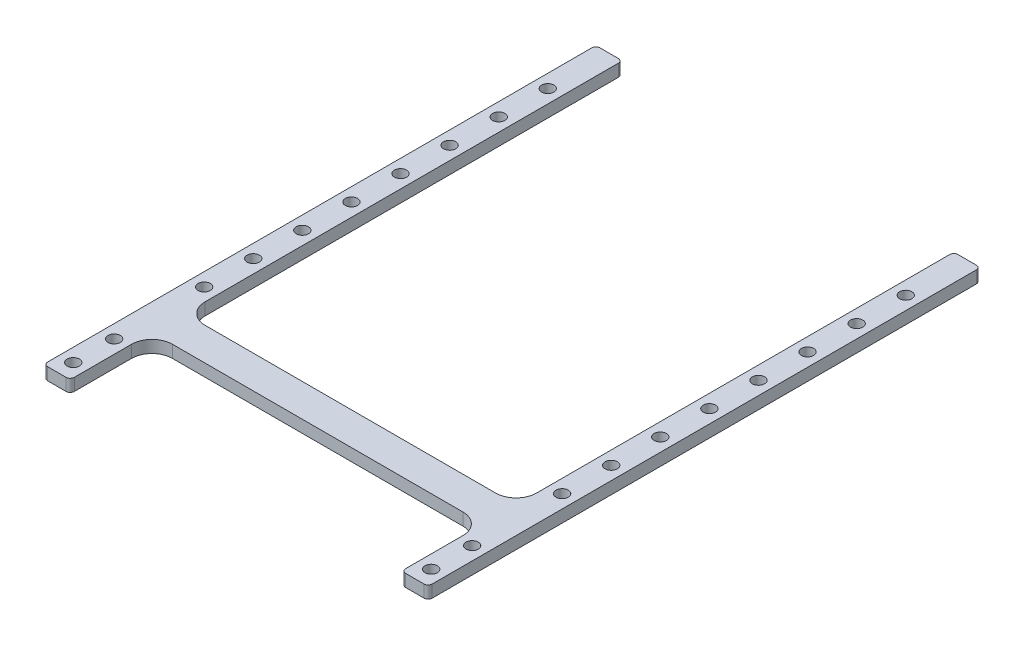
SolidWorks part; units mm, degrees
ref_plane "Front Plane" through (0, 0, 0) normal (0, 0, 1) x (1, 0, 0)
ref_plane "Top Plane" through (0, 0, 0) normal (0, 1, 0) x (1, 0, 0)
ref_plane "Right Plane" through (0, 0, 0) normal (1, 0, 0) x (0, 0, -1)
sketch "Sketch1" plane through (0, 0, 0) normal (0, 1, 0) x (1, 0, 0)
  line L6 (-221.7997, -37.6745) -> (-221.7997, -32.6745) construction
  line L9 (-226.7997, -52.6745) -> (-233.2997, -52.6745)
  line L10 (-233.2997, 67.3255) -> (-233.2997, -52.6745)
  line L13 (-145.7997, -52.6745) -> (-139.2997, -52.6745)
  line L14 (-139.2997, 67.3255) -> (-139.2997, -52.6745)
  line L23 (-150.7997, -37.6745) -> (-150.7997, -32.6745) construction
  line L25 (-226.7997, -37.6745) -> (-221.7997, -37.6745) construction
  line L26 (-186.2997, -37.6745) -> (-186.2997, -32.6745) construction
  line L27 (-221.7997, -24.6745) -> (-221.7997, -19.6745) construction
  line L28 (-221.7997, -19.6745) -> (-150.7997, -19.6745) construction
  line L29 (-150.7997, -19.6745) -> (-150.7997, -24.6745) construction
  line L30 (-145.7997, -52.6745) -> (-145.7997, -37.6745)
  line L31 (-226.7997, -52.6745) -> (-226.7997, -37.6745)
  line L32 (-226.7997, 67.3255) -> (-226.7997, -19.6745)
  line L33 (-145.7997, 67.3255) -> (-145.7997, -19.6745)
  line L34 (-150.7997, -19.6745) -> (-145.7997, -19.6745) construction
  line L35 (-221.7997, -19.6745) -> (-226.7997, -19.6745) construction
  line L36 (-221.7997, -37.6745) -> (-150.7997, -37.6745) construction
  line L37 (-150.7997, -37.6745) -> (-145.7997, -37.6745) construction
  line L38 (-145.7997, 67.3255) -> (-145.7997, 82.3255)
  line L39 (-145.7997, 82.3255) -> (-139.2997, 82.3255)
  line L40 (-139.2997, 67.3255) -> (-139.2997, 82.3255)
  line L41 (-221.7997, -24.6745) -> (-150.7997, -24.6745)
  line L43 (-221.7997, -32.6745) -> (-150.7997, -32.6745)
  line L45 (-233.2997, 67.3255) -> (-233.2997, 82.3255)
  line L46 (-233.2997, 82.3255) -> (-226.7997, 82.3255)
  line L47 (-226.7997, 67.3255) -> (-226.7997, 82.3255)
  arc A4 (-221.7997, -24.6745) -> (-226.7997, -19.6745) centre (-221.7997, -19.6745) cw
  arc A5 (-226.7997, -37.6745) -> (-221.7997, -32.6745) centre (-221.7997, -37.6745) cw
  arc A6 (-150.7997, -32.6745) -> (-145.7997, -37.6745) centre (-150.7997, -37.6745) cw
  arc A7 (-150.7997, -24.6745) -> (-145.7997, -19.6745) centre (-150.7997, -19.6745) ccw
  point P0 (0, 0)
extrude "Boss-Extrude1" add sketch "Sketch1" along normal blind 3
fillet "Fillet1" radius 1 8 edges at (-226.7997, 1.5, 52.6745) (-233.2997, 1.5, 52.6745) (-145.7997, 1.5, 52.6745) (-139.2997, 1.5, 52.6745) (-226.7997, 1.5, -82.3255) (-233.2997, 1.5, -82.3255) (-145.7997, 1.5, -82.3255) (-139.2997, 1.5, -82.3255)
sketch "Sketch2" plane through (0, 3, 0) normal (0, 1, 0) x (1, 0, 0)
  line L0 (-230.0497, 55.3255) -> (-230.0497, 67.3255) construction
  line L2 (-230.0497, -52.6745) -> (-142.5497, -52.6745) construction
  line L3 (-232.2997, -52.6745) -> (-227.7997, -52.6745) construction
  line L4 (-144.7997, -52.6745) -> (-140.2997, -52.6745) construction
  line L5 (-186.2997, -52.6745) -> (-186.2997, 95.8489) construction
  line L6 (-230.0497, 55.3255) -> (-230.0497, 43.3255) construction
  line L7 (-142.5497, 55.3255) -> (-142.5497, 43.3255) construction
  line L8 (-230.0497, 43.3255) -> (-230.0497, 31.3255) construction
  line L9 (-142.5497, 43.3255) -> (-142.5497, 31.3255) construction
  line L10 (-230.0497, 31.3255) -> (-230.0497, 19.3255) construction
  line L11 (-142.5497, 31.3255) -> (-142.5497, 19.3255) construction
  line L12 (-230.0497, 19.3255) -> (-230.0497, 7.3255) construction
  line L13 (-142.5497, 19.3255) -> (-142.5497, 7.3255) construction
  line L14 (-230.0497, 7.3255) -> (-230.0497, -4.6745) construction
  line L15 (-142.5497, 7.3255) -> (-142.5497, -4.6745) construction
  line L16 (-230.0497, -52.6745) -> (-230.0497, -48.6745) construction
  line L17 (-142.5497, -52.6745) -> (-142.5497, -48.6745) construction
  line L18 (-230.0497, -48.6745) -> (-230.0497, -38.6745) construction
  line L19 (-142.5497, -48.6745) -> (-142.5497, -38.6745) construction
  line L20 (-230.0497, -4.6745) -> (-230.0497, -16.6745) construction
  line L21 (-142.5497, -4.6745) -> (-142.5497, -16.6745) construction
  line L22 (-142.5497, 55.3255) -> (-142.5497, 67.3255) construction
  circle A0 centre (-230.0497, 7.3255) radius 1.5
  circle A1 centre (-142.5497, 7.3255) radius 1.5
  circle A2 centre (-230.0497, 31.3255) radius 1.5
  circle A3 centre (-230.0497, 55.3255) radius 1.5
  circle A4 centre (-230.0497, 43.3255) radius 1.5
  circle A5 centre (-230.0497, 19.3255) radius 1.5
  circle A6 centre (-230.0497, -4.6745) radius 1.5
  circle A8 centre (-142.5497, -4.6745) radius 1.5
  circle A9 centre (-230.0497, -38.6745) radius 1.5
  circle A10 centre (-230.0497, -48.6745) radius 1.5
  circle A11 centre (-142.5497, -38.6745) radius 1.5
  circle A12 centre (-142.5497, -48.6745) radius 1.5
  circle A13 centre (-142.5497, 19.3255) radius 1.5
  circle A14 centre (-142.5497, 31.3255) radius 1.5
  circle A15 centre (-142.5497, 43.3255) radius 1.5
  circle A16 centre (-142.5497, 55.3255) radius 1.5
  circle A17 centre (-230.0497, -16.6745) radius 1.5
  circle A18 centre (-142.5497, -16.6745) radius 1.5
  circle A19 centre (-230.0497, 67.3255) radius 1.5
  circle A20 centre (-142.5497, 67.3255) radius 1.5
extrude "Cut-Extrude1" cut sketch "Sketch2" against normal up to surface (3 mm away) up to face at (-186.2997, 0, -0.3255)
